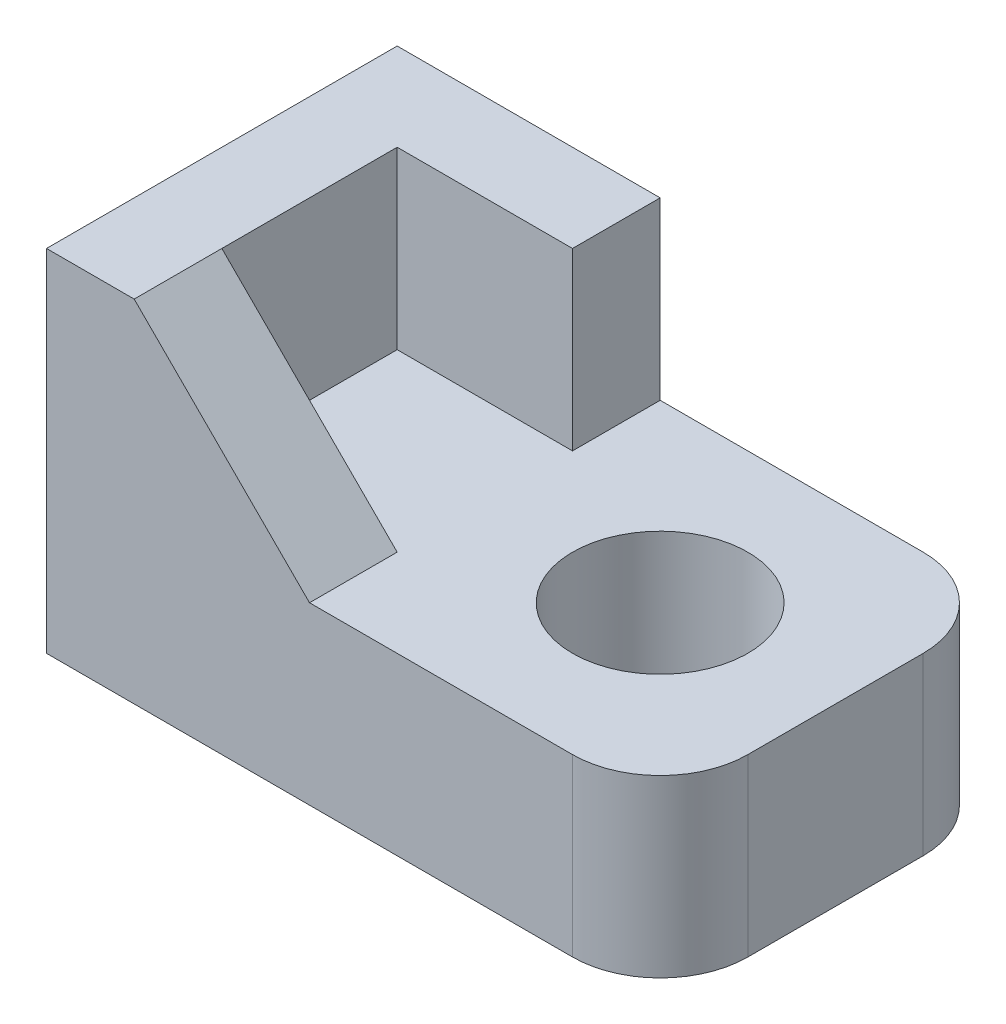
SolidWorks part; units mm, degrees
ref_plane "前基準面" through (0, 0, 0) normal (0, 0, 1) x (1, 0, 0)
ref_plane "上基準面" through (0, 0, 0) normal (0, 1, 0) x (1, 0, 0)
ref_plane "右基準面" through (0, 0, 0) normal (1, 0, 0) x (0, 0, -1)
sketch "草圖1" plane through (0, 0, 0) normal (0, 1, 0) x (1, 0, 0)
  line L0 (0, -13.2295) -> (0, 13.2295) construction
  line L1 (0, -10) -> (0, 10)
  line L2 (0, 10) -> (30, 10)
  line L3 (35, 5) -> (35, 0)
  line L4 (0, 0) -> (41.0198, 0) construction
  line L5 (25, 11.7564) -> (25, -5.1275) construction
  line L6 (25, -11.7564) -> (25, 5.1275) construction
  line L7 (0, -10) -> (30, -10)
  line L8 (35, 0) -> (35, -5)
  circle A0 centre (25, 0) radius 5
  arc A1 (35, 5) -> (30, 10) centre (30, 5) ccw
  arc A2 (35, -5) -> (30, -10) centre (30, -5) cw
  point P13 (35, 10)
  point P21 (35, -10)
  dimension "D4" = 10
  dimension "D5" = 5
  dimension "D1" = 10
  dimension "D2" = 35
  dimension "D3" = 10
extrude "填料-伸長1" add sketch "草圖1" along normal blind 10
sketch "草圖4" plane through (0, 0, 0) normal (0, 1, 0) x (1, 0, 0)
  line L0 (0, 0) -> (40.3797, 0) construction
  line L1 (0, 10) -> (0, -10) construction
  line L2 (0, 0) -> (0, 10)
  line L3 (0, 10) -> (15, 10)
  line L4 (30, 10) -> (0, 10) construction
  line L5 (15, 10) -> (15, 5)
  line L6 (15, 5) -> (5, 5)
  line L7 (5, 5) -> (5, -5)
  line L8 (5, -5) -> (15, -5)
  line L9 (15, -5) -> (15, -10)
  line L10 (0, -10) -> (30, -10) construction
  line L11 (15, -10) -> (0, -10)
  line L12 (0, -10) -> (0, 0)
  dimension "D1" = 15
  dimension "D2" = 5
  dimension "D3" = 10
  dimension "D4" = 10
  dimension "D5" = 10
extrude "填料-伸長2" add sketch "草圖4" along normal blind 20 contours L12 L2 L3 L5 L6 L7 L8 L9 L11
sketch "草圖5" plane through (0, 0, 10) normal (0, 0, 1) x (1, 0, 0)
  line L0 (15, 10) -> (5, 20)
  line L1 (15, 20) -> (0, 20) construction
  line L2 (5, 20) -> (15, 20)
  line L3 (15, 20) -> (15, 10)
  dimension "D1" = 10
extrude "除料-伸長1" cut sketch "草圖5" against normal blind 5
